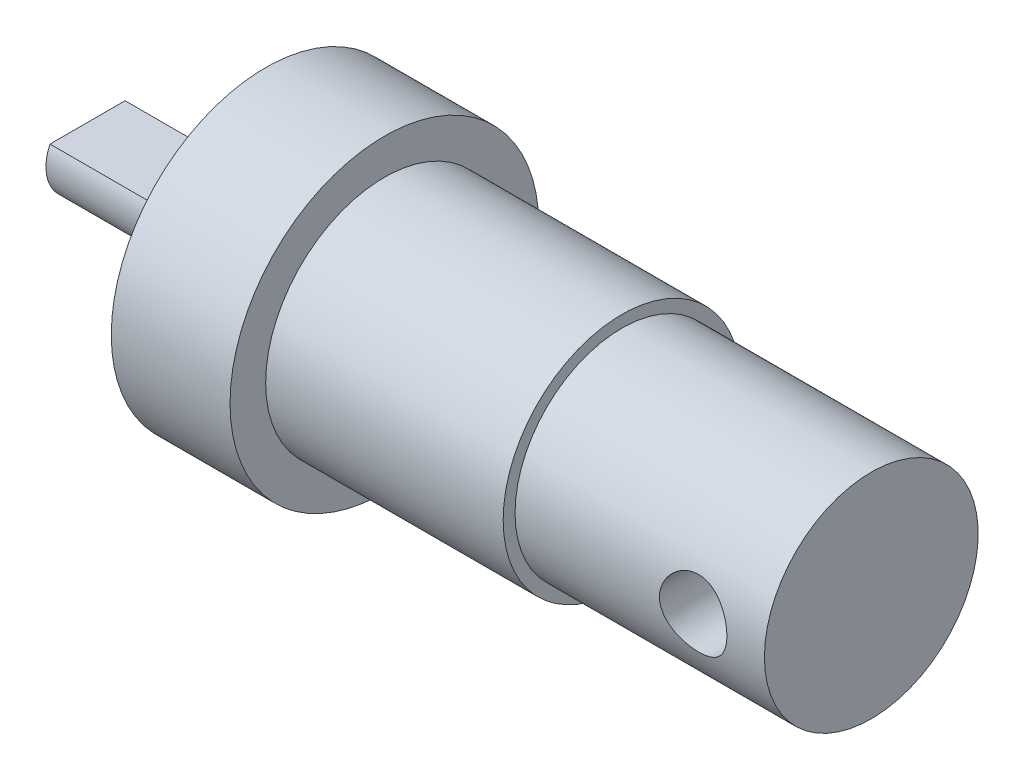
SolidWorks part; units mm, degrees
ref_plane "前视基准面" through (0, 0, 0) normal (0, 0, 1) x (1, 0, 0)
ref_plane "上视基准面" through (0, 0, 0) normal (0, 1, 0) x (1, 0, 0)
ref_plane "右视基准面" through (0, 0, 0) normal (1, 0, 0) x (0, 0, -1)
sketch "草图1" plane through (0, 0, 0) normal (0, 0, 1) x (1, 0, 0)
  line L0 (0, 0) -> (20.5, 0)
  line L1 (20.5, 0) -> (20.5, 4.5)
  line L2 (10, 5) -> (0, 5)
  line L3 (0, 5) -> (0, 6.5)
  line L4 (0, 6.5) -> (-5, 6.5)
  line L5 (-5, 6.5) -> (-5, 5)
  line L8 (-5, 0) -> (0, 0)
  line L9 (0, 5) -> (10, 5)
  line L10 (10, 5) -> (10, 4.5)
  line L11 (10, 4.5) -> (20.5, 4.5)
  line L12 (-5, 5) -> (-5, 0)
revolve "旋转1" add sketch "草图1" angle 360 about L8
ref_plane "基准面4" through (17.5, 0, 0) normal (1, 0, 0) x (0, 0, -1)
sketch "草图3" plane through (17.5, 0, 0) normal (1, 0, 0) x (0, 0, -1)
  line L0 (-6.6805, 0) -> (7.6, -0.0675) construction
  line L1 (-6.6805, 0) -> (-6.6805, 1.4075)
  line L2 (-6.6805, 1.4075) -> (7.6, 1.4075)
  line L3 (7.6, 1.4075) -> (7.6, -0.0675)
  line L4 (-6.6805, 0) -> (7.6, -0.0675)
revolve "切除-旋转1" cut sketch "草图3" angle 360 about L0
sketch "草图4" plane through (-5, 0, 0) normal (-1, 0, 0) x (0, 0, 1)
  line L3 (0, 0.75) -> (1.5811, 0.75)
  line L4 (0.0465, 0.75) -> (-1.5811, 0.75)
  arc A1 (-1.5811, 0.75) -> (1.5811, 0.75) centre (0, 0) ccw
extrude "凸台-拉伸2" add sketch "草图4" along normal blind 7.5 contours L4 A1 L3
